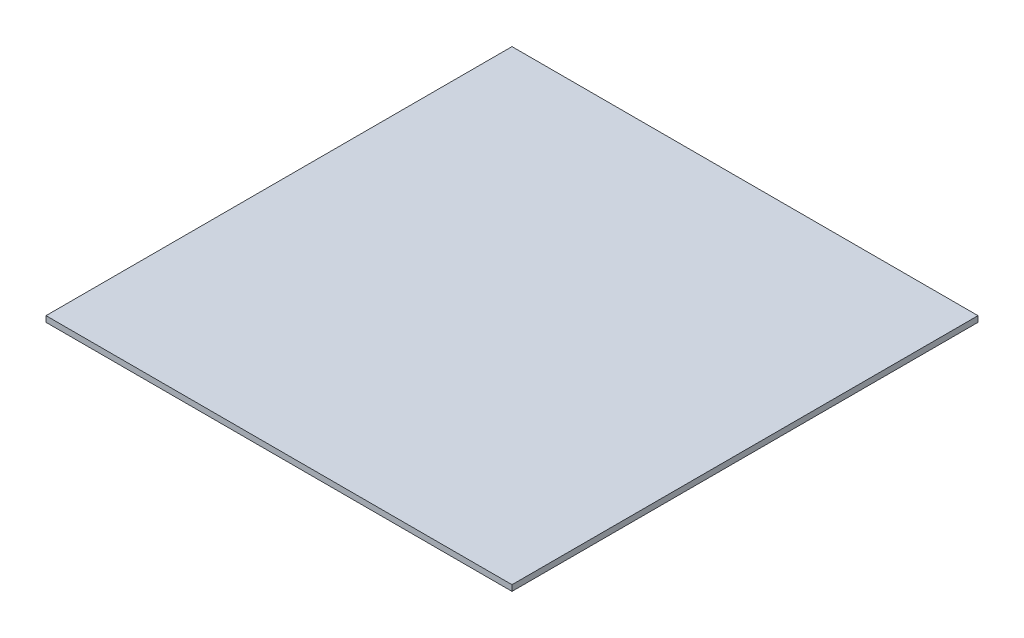
SolidWorks part; units mm, degrees
ref_plane "Front Plane" through (0, 0, 0) normal (0, 0, 1) x (1, 0, 0)
ref_plane "Top Plane" through (0, 0, 0) normal (0, 1, 0) x (1, 0, 0)
ref_plane "Right Plane" through (0, 0, 0) normal (1, 0, 0) x (0, 0, -1)
sketch "Sketch1" plane through (0, 0, 0) normal (0, 1, 0) x (1, 0, 0)
  line L1 (0, 0) -> (4000, 0)
  line L2 (0, 0) -> (0, 4000)
  line L3 (0, 4000) -> (4000, 4000)
  line L4 (4000, 0) -> (4000, 4000)
extrude "Boss-Extrude1" add sketch "Sketch1" along normal blind 50
